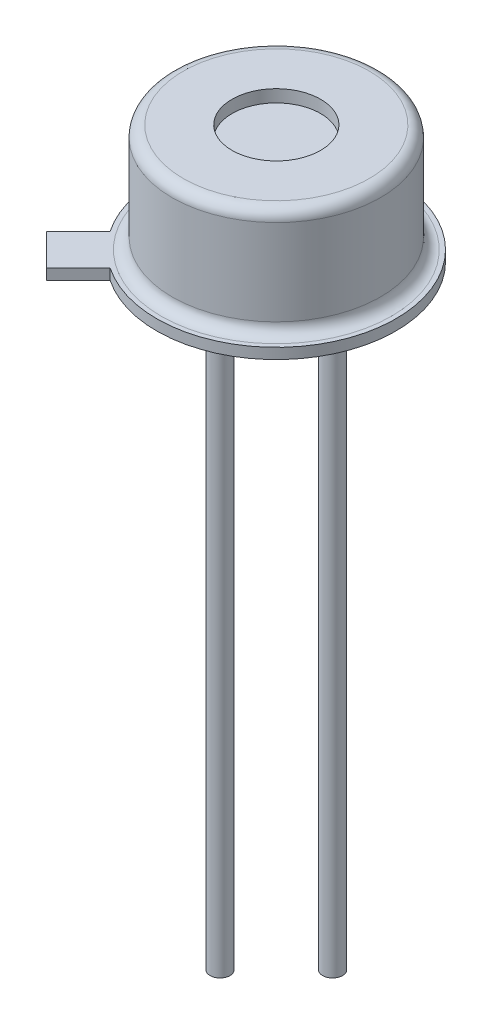
SolidWorks part; units mm, degrees
ref_plane "Front Plane" through (0, 0, 0) normal (0, 0, 1) x (1, 0, 0)
ref_plane "Top Plane" through (0, 0, 0) normal (0, 1, 0) x (1, 0, 0)
ref_plane "Right Plane" through (0, 0, 0) normal (1, 0, 0) x (0, 0, -1)
sketch "Sketch1" plane through (0, 0, 0) normal (0, 1, 0) x (1, 0, 0)
  line L0 (-2.2343, -1.5159) -> (-2.9527, -2.2343)
  line L1 (-2.9527, -2.2343) -> (-2.2343, -2.9527)
  line L2 (-2.2343, -2.9527) -> (-1.5159, -2.2343)
  line L3 (0, 0) -> (-2.5935, -2.5935) construction
  line L4 (0, -55) -> (0, 55) construction
  arc A0 (-1.5159, -2.2343) -> (-2.2343, -1.5159) centre (0, 0) ccw
  dimension "D3" = 2.7
  dimension "D1" = 45
  dimension "D2" = 1.016
  dimension "D4" = 1.016
extrude "Boss-Extrude1" add sketch "Sketch1" along normal blind 0.24
sketch "Sketch3" plane through (0, 0.24, 0) normal (0, 1, 0) x (1, 0, 0)
  circle A0 centre (0, 0) radius 2.35
  dimension "D1" = 4.7
extrude "Boss-Extrude2" add sketch "Sketch3" along normal blind 2.44
sketch "Sketch4" plane through (0, 2.68, 0) normal (0, 1, 0) x (1, 0, 0)
  circle A0 centre (0, 0) radius 1
  dimension "D1" = 2
extrude "Cut-Extrude1" cut sketch "Sketch4" against normal blind 0.2794
sketch "Sketch6" plane through (0, 0, 0) normal (0, -1, 0) x (1, 0, 0)
  circle A0 centre (0, 1.27) radius 0.225
  circle A1 centre (0, -1.27) radius 0.225
  circle A2 centre (1.27, 0) radius 0.225
  circle A3 centre (0, 0) radius 1.27 construction
  circle A4 centre (0, 0) radius 1.495 construction
  dimension "D1" = 0.45
  dimension "D2" = 2.54
extrude "Boss-Extrude3" add sketch "Sketch6" along normal blind 13.2
sketch "Sketch7" plane through (-2.5935, 0, 2.5935) normal (-0.7071, 0, 0.7071) x (0.7071, 0, 0.7071)
  line L4 (-0.508, 0) -> (0.508, 0)
  line L5 (0.508, 0) -> (0.508, 0.24)
  line L6 (0.508, 0.24) -> (-0.508, 0.24)
  line L7 (-0.508, 0.24) -> (-0.508, 0)
  line L8 (-0.508, 0) -> (0.508, 0)
  line L9 (0.508, 0) -> (0.508, 0.24)
  line L10 (0.508, 0.24) -> (-0.508, 0.24)
  line L11 (-0.508, 0.24) -> (-0.508, 0)
  dimension "D1" = 0
extrude "Cut-Extrude3" [suppressed] cut sketch "Sketch7" against normal up to vertex
fillet "Fillet1" radius 0.25 2 edges at (0, 2.68, 2.35) (0, 0.24, 2.35)
sketch "Sketch5" plane through (0, 2.4006, 0) normal (0, 1, 0) x (1, 0, 0)
  circle A0 centre (0, 0) radius 0.875
  dimension "D1" = 1.75
extrude "Window thickness" [suppressed] cut sketch "Sketch5" against normal offset from surface (0.6106 mm away) 1.79
sketch "Sketch10" plane through (0, 0, 0) normal (0, -1, 0) x (1, 0, 0)
  circle A0 centre (0, -1.27) radius 0.6
  circle A1 centre (0, 1.27) radius 0.6
  circle A2 centre (0, 1.27) radius 0.225 construction
  circle A3 centre (0, -1.27) radius 0.225 construction
  dimension "D1" = 1.2
split line "Split Line1"
